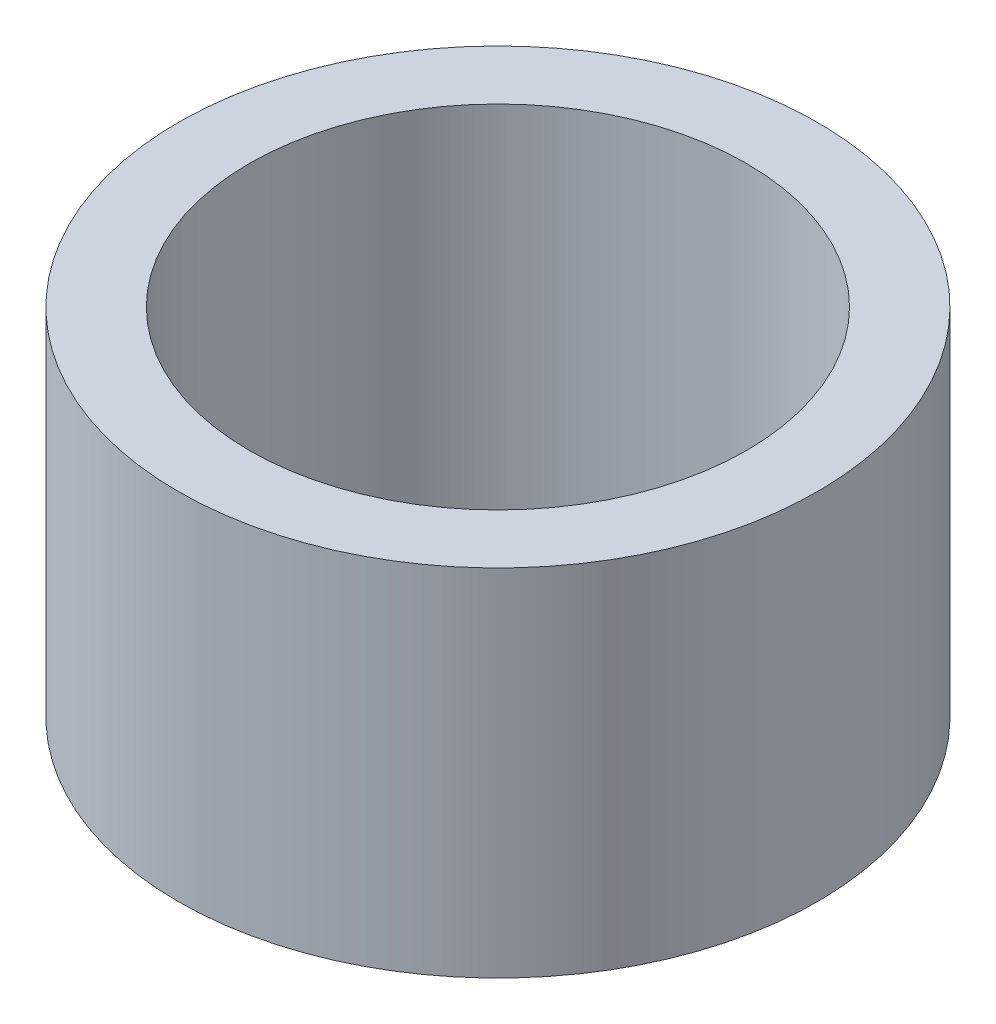
SolidWorks part; units mm, degrees
ref_plane "Спереди" through (0, 0, 0) normal (0, 0, 1) x (1, 0, 0)
ref_plane "Сверху" through (0, 0, 0) normal (0, 1, 0) x (1, 0, 0)
ref_plane "Справа" through (0, 0, 0) normal (1, 0, 0) x (0, 0, -1)
sketch "Эскиз1" plane through (0, 0, 0) normal (0, 1, 0) x (1, 0, 0)
  circle A0 centre (0, 0) radius 45
  circle A1 centre (0, 0) radius 35
  dimension "D1" = 90
  dimension "D2" = 70
extrude "Бобышка-Вытянуть1" add sketch "Эскиз1" along normal blind 50
